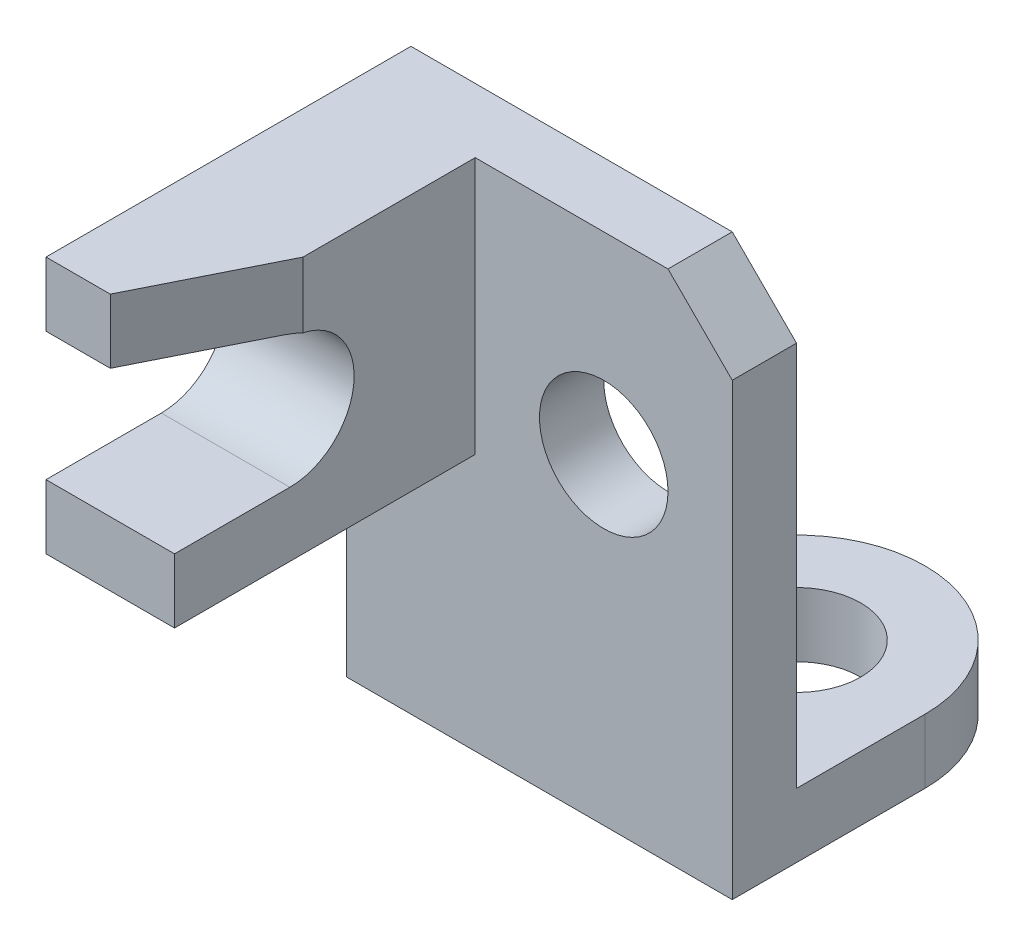
SolidWorks part; units mm, degrees
ref_plane "Front Plane" through (0, 0, 0) normal (0, 0, 1) x (1, 0, 0)
ref_plane "Top Plane" through (0, 0, 0) normal (0, 1, 0) x (1, 0, 0)
ref_plane "Right Plane" through (0, 0, 0) normal (1, 0, 0) x (0, 0, -1)
sketch "Sketch1" plane through (0, 0, 0) normal (0, 0, 1) x (1, 0, 0)
  line L0 (5, 8) -> (6, 7)
  line L1 (0, 0) -> (6, 0)
  line L2 (0, 0) -> (0, 8)
  line L3 (0, 8) -> (5, 8)
  line L4 (6, 0) -> (6, 7)
  circle A0 centre (4, 5) radius 1
  point P1 (6, 8)
  point P11 (6, 4.8338)
  point P12 (-2.2132, 11.719)
  dimension "D6" = 2
  dimension "D1" = 8
  dimension "D2" = 6
  dimension "D3" = 5
  dimension "D4" = 2
extrude "Boss-Extrude1" add sketch "Sketch1" against normal blind 1
sketch "Sketch2" plane through (0, 0, 0) normal (0, -1, 0) x (1, 0, 0)
  line L0 (6, -1) -> (6, -2.9993)
  line L1 (2, -2.9993) -> (2, -1)
  line L2 (5, -1) -> (0, -1) construction
  line L3 (2, -1) -> (6, -1)
  arc A0 (6, -2.9993) -> (2, -2.9993) centre (4, -2.9993) cw
  circle A1 centre (4, -2.9993) radius 1
  dimension "D2" = 2
  dimension "D3" = 2
  dimension "D1" = 1.9993
extrude "Boss-Extrude2" add sketch "Sketch2" against normal blind 1
sketch "Sketch3" plane through (0, 0, 0) normal (-1, 0, 0) x (0, 0, 1)
  line L0 (0, 8) -> (0, 4)
  line L1 (0, 0) -> (0, 7) construction
  line L2 (0, 4) -> (4.6788, 4)
  line L3 (4.6788, 4) -> (4.6788, 5)
  line L4 (4.6788, 5) -> (2.8842, 5)
  line L5 (2.8842, 7) -> (4.6788, 7)
  line L6 (4.6788, 7) -> (4.6788, 8)
  line L7 (4.6788, 8) -> (0, 8)
  arc A0 (2.8842, 5) -> (2.8842, 7) centre (2.8842, 6) cw
  dimension "D3" = 1
  dimension "D1" = 1
  dimension "D2" = 1
extrude "Boss-Extrude3" add sketch "Sketch3" against normal blind 2
sketch "Sketch4" plane through (0, 8, 0) normal (0, 1, 0) x (1, 0, 0)
  line L0 (1, -4.6788) -> (2, -2.6788)
  line L1 (2, -4.6788) -> (0, -4.6788) construction
  line L2 (2, -4.6788) -> (2, 0) construction
  line L3 (2, -2.6788) -> (2, -4.6788)
  line L4 (2, -4.6788) -> (1, -4.6788)
  dimension "D1" = 2
extrude "Cut-Extrude1" cut sketch "Sketch4" against normal blind 2
